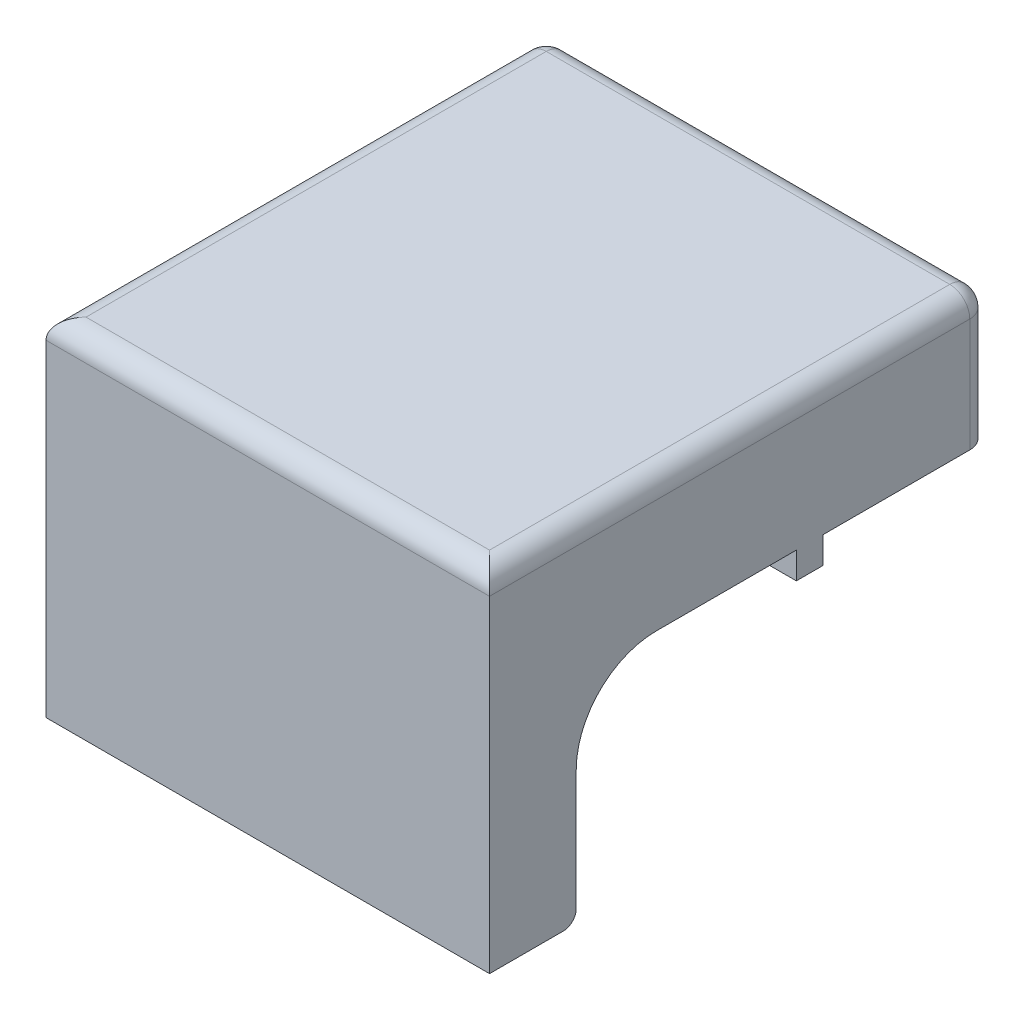
SolidWorks part; units mm, degrees
ref_plane "Front Plane" through (0, 0, 0) normal (0, 0, 1) x (1, 0, 0)
ref_plane "Top Plane" through (0, 0, 0) normal (0, 1, 0) x (1, 0, 0)
ref_plane "Right Plane" through (0, 0, 0) normal (1, 0, 0) x (0, 0, -1)
sketch "Sketch1" plane through (0, 0, 0) normal (0, 1, 0) x (1, 0, 0)
  line L0 (0, 0) -> (-43.5, 0)
  line L1 (-43.5, 0) -> (-43.5, -68)
  line L2 (-43.5, -68) -> (23, -68)
  line L3 (23, -68) -> (23, 0)
  line L6 (0, 0) -> (23, 0)
  dimension "D1" = 43.5
  dimension "D3" = 68
  dimension "D4" = 66.5
extrude "Boss-Extrude1" add sketch "Sketch1" along normal blind 10
sketch "Sketch2" plane through (0, 0, 0) normal (0, -1, 0) x (1, 0, 0)
  line L0 (-43.5, 68) -> (-43.5, 62)
  line L1 (-43.5, 0) -> (-43.5, 68) construction
  line L2 (-43.5, 62) -> (23, 62)
  line L3 (23, 68) -> (23, 0) construction
  line L4 (23, 62) -> (23, 68)
  line L6 (-43.5, 68) -> (-43.5, 75)
  line L7 (-43.5, 75) -> (23, 75)
  line L8 (23, 75) -> (23, 68)
  dimension "D1" = 6
  dimension "D2" = 7
extrude "Boss-Extrude2" add sketch "Sketch2" along normal blind 42 and the other way blind 10
sketch "Sketch4" plane through (0, 0, 0) normal (0, -1, 0) x (1, 0, 0)
  line L0 (-43.5, 62) -> (-36, 62)
  line L1 (-43.5, 62) -> (23, 62) construction
  line L5 (-43.5, 0) -> (-43.5, 62)
  line L6 (23, 0) -> (23, 62)
  line L7 (23, 62) -> (15.5, 62)
  line L8 (-43.5, 62) -> (23, 62) construction
  line L13 (-36, 62) -> (-36, 7.5)
  line L14 (-36, 7.5) -> (15.5, 7.5)
  line L15 (15.5, 7.5) -> (15.5, 62)
  line L16 (-43.5, 0) -> (23, 0)
  dimension "D1" = 7.5
  dimension "D2" = 7.5
  dimension "D3" = 7.5
extrude "Boss-Extrude3" add sketch "Sketch4" along normal blind 10
sketch "Sketch3" plane through (0, 0, 0) normal (0, 0, -1) x (-1, 0, 0)
  line L0 (-23, 10) -> (43.5, 10) construction
  line L1 (43.5, 10) -> (43.5, -10) construction
  circle A0 centre (16, -22) radius 20.035
  dimension "D1" = 32
  dimension "D2" = 40.07
  dimension "D3" = 27.5
extrude "Cut-Extrude2" cut sketch "Sketch3" against normal blind 10
fillet "Fillet1" radius 12 2 edges at (-39.75, -10, 62) (19.25, -10, 62)
sketch "Sketch9" plane through (0, -10, 0) normal (0, -1, 0) x (1, 0, 0)
  line L0 (-43.5, 50) -> (-43.5, 0) construction
  line L1 (-43.5, 25) -> (-36, 25)
  line L2 (-43.5, 25) -> (-43.5, 29)
  line L3 (-43.5, 29) -> (-36, 29)
  line L4 (-36, 25) -> (-36, 29)
  line L5 (-36, 7.5) -> (-36, 62) construction
  line L6 (23, 0) -> (23, 50) construction
  line L7 (23, 25) -> (15.5, 25)
  line L8 (23, 25) -> (23, 29)
  line L9 (23, 29) -> (15.5, 29)
  line L10 (15.5, 25) -> (15.5, 29)
  line L11 (15.5, 50) -> (15.5, 7.5) construction
  line L12 (-43.5, 0) -> (-32.0437, 0) construction
  line L13 (0.0437, 0) -> (23, 0) construction
  dimension "D1" = 4
  dimension "D2" = 4
  dimension "D3" = 25
  dimension "D4" = 25
extrude "Boss-Extrude5" add sketch "Sketch9" along normal blind 4
fillet "Fillet4" radius 1.95 1 edges at (-10.25, -42, 62)
fillet "Fillet5" radius 3 2 edges at (23, 0, 0) (-43.5, 0, 0)
fillet "Fillet6" radius 3 6 edges at (-10.25, 10, 75) (-43.5, 10, 39) (-42.6213, 10, 0.8787) (-10.25, 10, 0) (22.1213, 10, 0.8787) (23, 10, 39)
sketch "Sketch10" plane through (0, -42, 0) normal (0, -1, 0) x (1, 0, 0)
  line L0 (23, 75) -> (-43.5, 75) construction
  line L1 (-43.5, 75) -> (-43.5, 63.95) construction
  line L2 (23, 63.95) -> (23, 75) construction
  circle A0 centre (-28.5, 68) radius 3
  circle A1 centre (5.5, 68) radius 3
  point P6 (0, 0)
  point P8 (-38.6733, 70.627)
  point P12 (0, 0)
  dimension "D1" = 6
  dimension "D3" = 7
  dimension "D4" = 15
  dimension "D5" = 17.5
extrude "Cut-Extrude3" cut sketch "Sketch10" against normal blind 10
